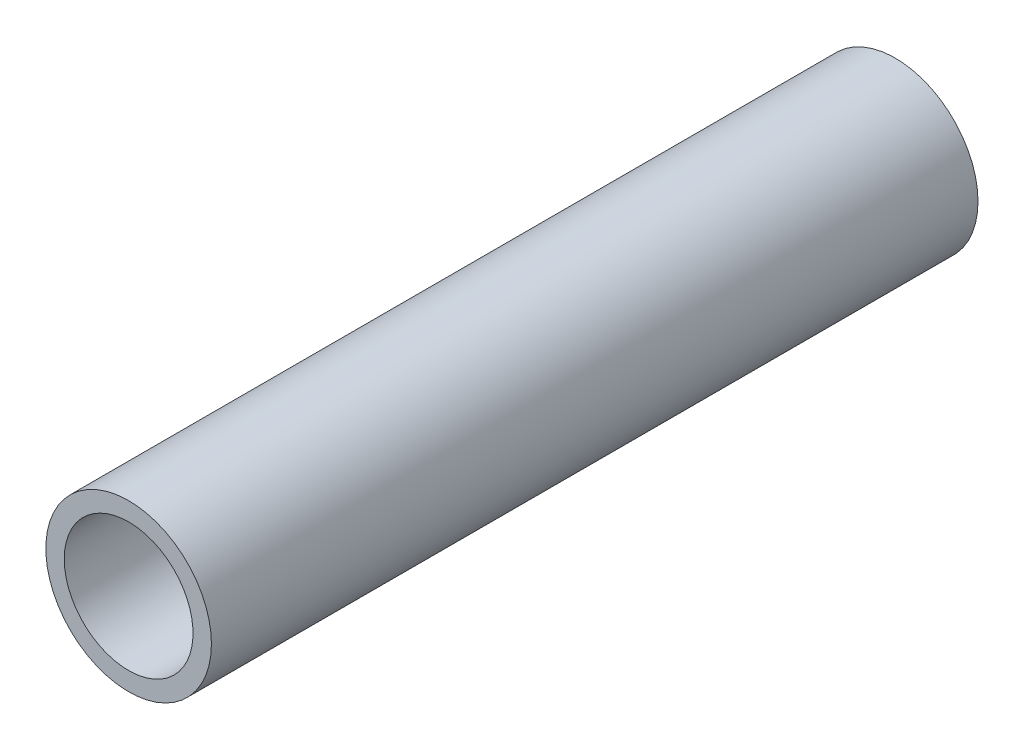
SolidWorks part; units mm, degrees
material "Plain Carbon Steel"
ref_plane "Front" through (0, 0, 0) normal (0, 0, 1) x (1, 0, 0)
ref_plane "Top" through (0, 0, 0) normal (0, 1, 0) x (1, 0, 0)
ref_plane "Right" through (0, 0, 0) normal (1, 0, 0) x (0, 0, -1)
sketch "Sketch1" plane through (0, 0, 0) normal (0, 0, 1) x (1, 0, 0)
  circle A0 centre (-7.3192, 4.997) radius 13.716
  dimension "D1" = 27.432
extrude "Boss-Extrude1" add sketch "Sketch1" along normal blind 127
sketch "Sketch2" plane through (0, 0, 0) normal (0, 0, -1) x (-1, 0, 0)
  circle A0 centre (7.3192, 4.997) radius 10.668
  dimension "D1" = 21.336
extrude "Cut-Extrude1" cut sketch "Sketch2" against normal blind 127
scale "Scale1" scale about centroid uniform scaling yes scale factor 0.735294
scale "Scale2" scale about centroid uniform scaling yes scale factor 0.892857
scale "Scale3" scale about centroid uniform scaling yes scale factor 1.056338
